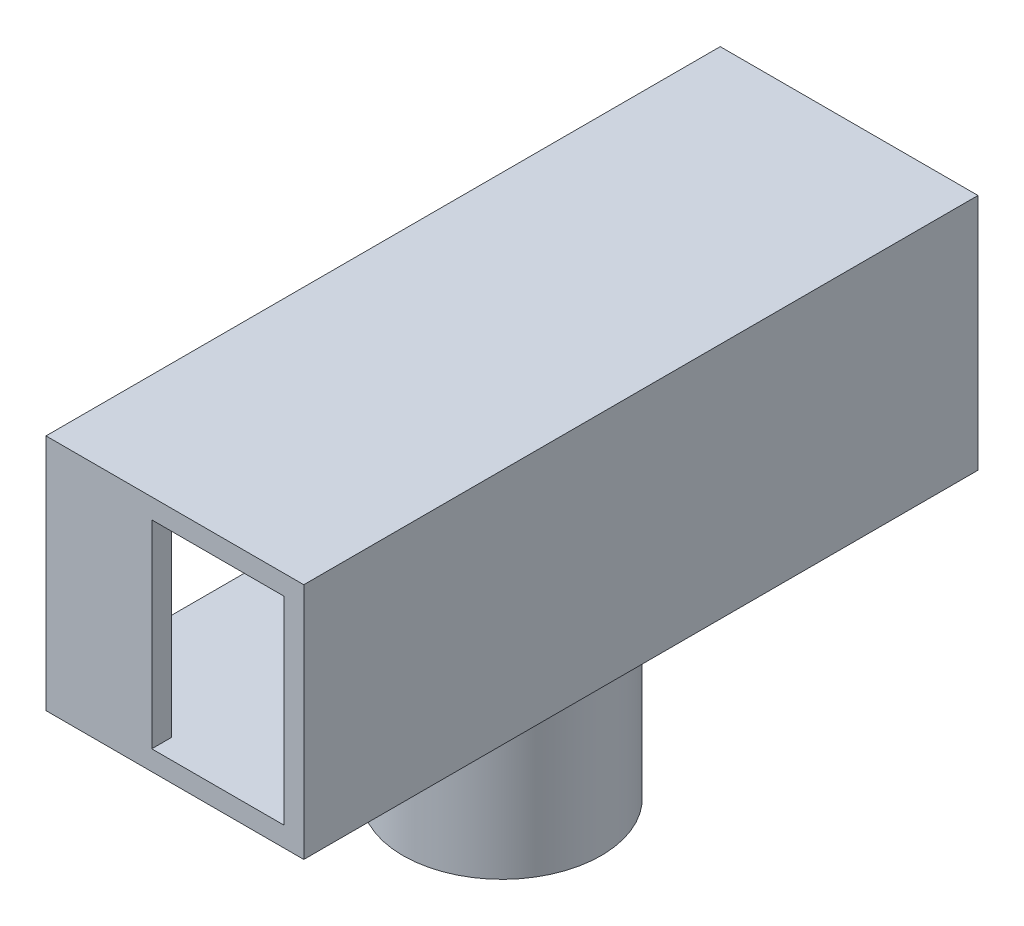
SolidWorks part; units mm, degrees
ref_plane "前视基准面" through (0, 0, 0) normal (0, 0, 1) x (1, 0, 0)
ref_plane "上视基准面" through (0, 0, 0) normal (0, 1, 0) x (1, 0, 0)
ref_plane "右视基准面" through (0, 0, 0) normal (1, 0, 0) x (0, 0, -1)
other "Configuration Table"
sketch "草图1" plane through (0, 0, 0) normal (0, 1, 0) x (1, 0, 0)
  circle A0 centre (0, 0) radius 6
extrude "凸台-拉伸1" add sketch "草图1" along normal blind 1.5
sketch "草图2" plane through (0, 1.5, 0) normal (0, 1, 0) x (1, 0, 0)
  circle A0 centre (0, 0) radius 6
extrude "凸台-拉伸2" add sketch "草图2" along normal blind 14
sketch "草图3" plane through (0, 15.5, 0) normal (0, 1, 0) x (1, 0, 0)
  line L1 (-9, 24) -> (9, 24)
  line L2 (-9, 24) -> (-9, -24)
  line L3 (-9, -24) -> (9, -24)
  line L4 (9, 24) -> (9, -24)
  line L5 (-9, 24) -> (9, -24) construction
  line L6 (-9, -24) -> (9, 24) construction
  point P0 (0, 0)
  dimension "D1" = 18
  dimension "D2" = 48
extrude "凸台-拉伸3" add sketch "草图3" along normal blind 15
shell "抽壳3" thickness 1.5
sketch "草图4" plane through (0, 0, 24) normal (0, 0, -1) x (-1, 0, 0)
  line L0 (-9, 15.5) -> (-9, 30.5)
  line L1 (-9, 30.5) -> (1, 30.5)
  line L2 (1, 30.5) -> (1, 15.5)
  line L3 (1, 15.5) -> (-9, 15.5)
  line L4 (-9, 15.5) -> (9, 15.5)
  line L5 (9, 15.5) -> (9, 30.5)
  line L6 (9, 30.5) -> (-9, 30.5)
  line L7 (-9, 30.5) -> (-9, 15.5)
  line L8 (-9, 15.5) -> (9, 15.5) construction
  line L9 (9, 15.5) -> (9, 30.5) construction
  line L10 (9, 30.5) -> (-9, 30.5) construction
  line L11 (-9, 30.5) -> (-9, 15.5) construction
  dimension "D2" = 10
  dimension "D1" = 0
extrude "切除-拉伸1" cut sketch "草图4" against normal blind 15
sketch "草图6" plane through (-9, 0, 0) normal (-1, 0, 0) x (0, 0, 1)
  line L0 (-24, 30.5) -> (-24, 15.5) construction
  line L1 (-24, 30.5) -> (24, 30.5) construction
  line L2 (-24, 30.5) -> (-24, 15.5)
  line L3 (-24, 30.5) -> (24, 30.5)
  line L4 (-25.5, 14) -> (25.5, 14)
  line L5 (25.5, 14) -> (25.5, 32)
  line L6 (25.5, 32) -> (-25.5, 32)
  line L7 (-25.5, 32) -> (-25.5, 14)
  line L8 (-25.5, 14) -> (25.5, 14)
  line L9 (25.5, 14) -> (25.5, 32)
  line L10 (25.5, 32) -> (-25.5, 32)
  line L11 (-25.5, 32) -> (-25.5, 14)
  dimension "D2" = 18
  dimension "D1" = 0
